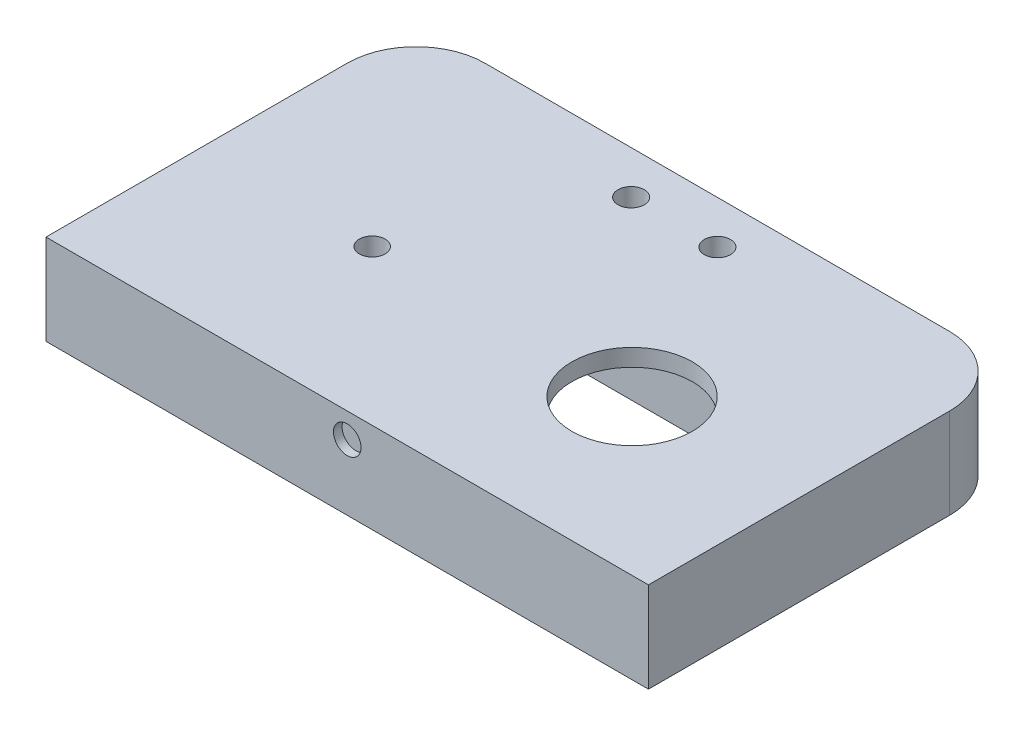
SolidWorks part; units mm, degrees
ref_plane "前视基准面" through (0, 0, 0) normal (0, 0, 1) x (1, 0, 0)
ref_plane "上视基准面" through (0, 0, 0) normal (0, 1, 0) x (1, 0, 0)
ref_plane "右视基准面" through (0, 0, 0) normal (1, 0, 0) x (0, 0, -1)
sketch "草图1" plane through (0, 0, 0) normal (0, 1, 0) x (1, 0, 0)
  line L0 (-35, -18) -> (35, -18)
  line L1 (-35, 25) -> (35, 25)
  line L2 (-35, 25) -> (-35, -18)
  line L4 (35, 25) -> (35, -18)
  line L5 (-35, 25) -> (35, -25) construction
  line L6 (-35, -25) -> (35, 25) construction
  point P0 (0, 0)
  dimension "D1" = 70
  dimension "D2" = 43
extrude "凸台-拉伸1" add sketch "草图1" along normal blind 10.5
sketch "草图2" plane through (0, 10.5, 0) normal (0, 1, 0) x (1, 0, 0)
  line L0 (0, -55) -> (0, 55) construction
  circle A0 centre (15.1, 0) radius 1.5
  circle A1 centre (-15.1, 0) radius 1.5
  dimension "D2" = 3
  dimension "D1" = 15.1
extrude "切除-拉伸1" cut sketch "草图2" against normal blind 15
sketch "草图3" plane through (0, 0, 0) normal (0, -1, 0) x (1, 0, 0)
  line L1 (25.6, -10.1) -> (-15.4, -10.1)
  line L2 (25.6, -10.1) -> (25.6, 10.1)
  line L3 (25.6, 10.1) -> (-15.4, 10.1)
  line L4 (-15.4, -10.1) -> (-15.4, 10.1)
  line L5 (25.6, -10.1) -> (-15.4, 10.1) construction
  line L6 (25.6, 10.1) -> (-15.4, -10.1) construction
  circle A0 centre (15.1, 0) radius 1.5 construction
  circle A1 centre (15.1, 0) radius 1.5 construction
  point P0 (5.1, 0)
  dimension "D1" = 41
  dimension "D2" = 20.2
  dimension "D3" = 10.5
extrude "切除-拉伸2" cut sketch "草图3" against normal blind 6
sketch "草图4" plane through (0, 6, 0) normal (0, -1, 0) x (1, 0, 0)
  circle A0 centre (15.1, 0) radius 7
  dimension "D1" = 14
extrude "切除-拉伸3" cut sketch "草图4" against normal blind 8.5
sketch "草图6" plane through (0, 6, 0) normal (0, -1, 0) x (1, 0, 0)
  line L0 (25.6, 10.1) -> (-15.4, 10.1) construction
  line L1 (-13.4, 10.1) -> (25.6, 10.1)
  line L2 (-13.4, 10.1) -> (-13.4, -10.1)
  line L3 (-13.4, -10.1) -> (25.6, -10.1)
  line L4 (25.6, 10.1) -> (25.6, -10.1)
  line L5 (-15.4, -1.4697) -> (-15.4, -10.1) construction
  dimension "D1" = 2
extrude "切除-拉伸4" cut sketch "草图6" against normal blind 2.5
sketch "草图7" plane through (0, 0, 0) normal (0, -1, 0) x (1, 0, 0)
  line L0 (25.6, -10.1) -> (25.6, 10.1) construction
  line L1 (6.1, 10.1) -> (6.1, 15.1559) construction
  line L2 (25.6, 10.1) -> (-13.4, 10.1) construction
  line L3 (55, 0) -> (-55, 0) construction
  line L4 (5.1, 10.1) -> (5.1, 15.7097) construction
  line L5 (25.6, 10.1) -> (-15.4, 10.1) construction
  circle A0 centre (29.2, 5) radius 1.525
  circle A1 centre (29.2, -5) radius 1.525
  circle A2 centre (-19, -5) radius 1.525
  circle A3 centre (-19, 5) radius 1.525
  dimension "D1" = 3.05
  dimension "D2" = 5
  dimension "D3" = 3.6
  dimension "D4" = 20.5
extrude "切除-拉伸5" cut sketch "草图7" against normal blind 5
sketch "草图9" plane through (0, 0, 0) normal (0, -1, 0) x (1, 0, 0)
  line L0 (25.6, -10.1) -> (25.6, 10.1) construction
  line L1 (-22.4, 0.9) -> (32.6, 0.9)
  line L2 (-22.4, 0.9) -> (-22.4, -0.9)
  line L3 (-22.4, -0.9) -> (32.6, -0.9)
  line L4 (32.6, 0.9) -> (32.6, -0.9)
  line L5 (-22.4, 0.9) -> (32.6, -0.9) construction
  line L6 (-22.4, -0.9) -> (32.6, 0.9) construction
  line L7 (-15.4, 10.1) -> (-15.4, 1.4697) construction
  point P0 (5.1, 0)
  dimension "D1" = 7
  dimension "D2" = 7
  dimension "D3" = 1.8
extrude "切除-拉伸6" cut sketch "草图9" against normal blind 2
fillet "圆角1" radius 8 2 edges at (-35, 5.25, -25) (35, 5.25, -25)
sketch "草图10" plane through (0, 10.5, 0) normal (0, 1, 0) x (1, 0, 0)
  line L0 (0, 25) -> (0, -25) construction
  line L1 (27, 25) -> (-27, 25) construction
  line L2 (-27, -25) -> (27, -25) construction
  circle A0 centre (15.1, 0) radius 7 construction
  circle A1 centre (15.1, 0) radius 7
  circle A2 centre (-15.1, 0) radius 1.5 construction
  circle A3 centre (-15.1, 0) radius 1.5
  circle A4 centre (-5.0124, 20) radius 1.525
  circle A5 centre (5.0124, 20) radius 1.525
  dimension "D1" = 3.05
  dimension "D2" = 22.4
  dimension "D3" = 5
extrude "切除-拉伸7" cut sketch "草图10" against normal blind 20
sketch "草图11" plane through (0, 0, 18) normal (0, 0, 1) x (1, 0, 0)
  circle A0 centre (0, 7.6074) radius 1.6
extrude "切除-拉伸8" cut sketch "草图11" against normal blind 1
